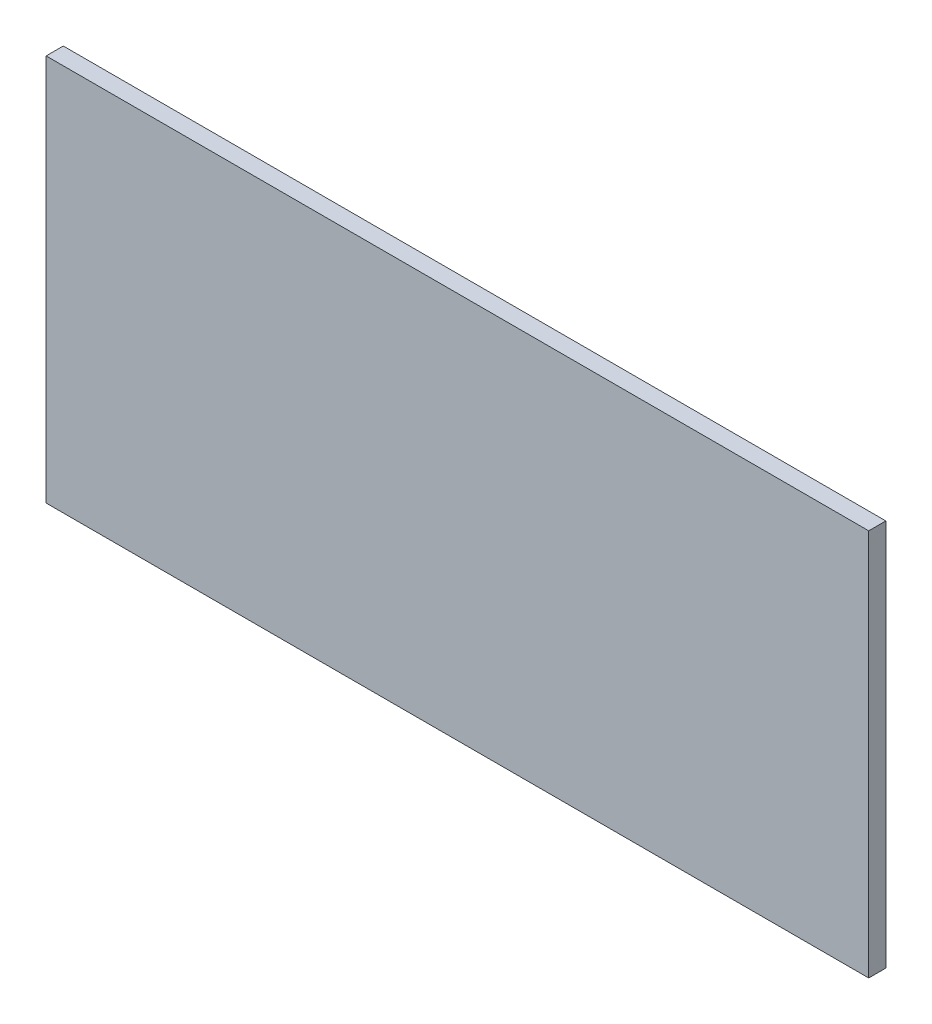
SolidWorks part; units mm, degrees
material "Pine"
ref_plane "Front" through (0, 0, 0) normal (0, 0, 1) x (1, 0, 0)
ref_plane "Top" through (0, 0, 0) normal (0, 1, 0) x (1, 0, 0)
ref_plane "Right" through (0, 0, 0) normal (1, 0, 0) x (0, 0, -1)
sketch "Sketch1" plane through (0, 0, 0) normal (0, 1, 0) x (1, 0, 0)
  line L1 (0, 0) -> (1219.2, 0)
  line L2 (0, 0) -> (0, 25.4)
  line L3 (0, 25.4) -> (1219.2, 25.4)
  line L4 (1219.2, 0) -> (1219.2, 25.4)
  dimension "D1" = 1219.2
  dimension "D2" = 25.4
extrude "Boss-Extrude1" add sketch "Sketch1" along normal blind 574
